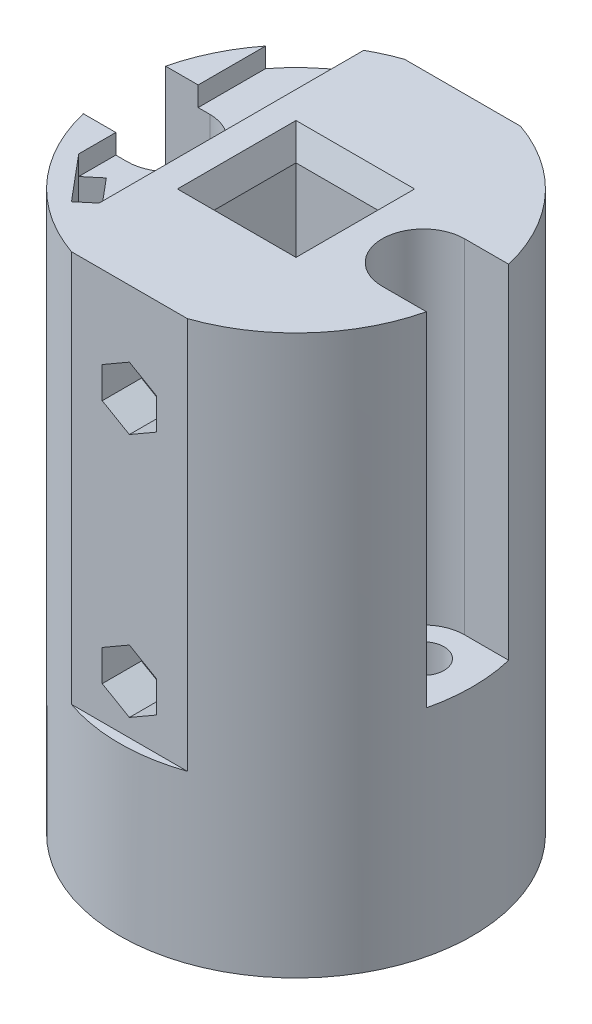
SolidWorks part; units mm, degrees
ref_plane "Спереди" through (0, 0, 0) normal (0, 0, 1) x (1, 0, 0)
ref_plane "Сверху" through (0, 0, 0) normal (0, 1, 0) x (1, 0, 0)
ref_plane "Справа" through (0, 0, 0) normal (1, 0, 0) x (0, 0, -1)
sketch "Sketch1" plane through (0, 0, 0) normal (0, 1, 0) x (1, 0, 0)
  line L0 (0, 0) -> (17.6067, 3.7424) construction
  line L1 (5.05, -5.05) -> (-5.05, -5.05)
  line L2 (5.05, -5.05) -> (5.05, 5.05)
  line L3 (5.05, 5.05) -> (-5.05, 5.05)
  line L4 (-5.05, -5.05) -> (-5.05, 5.05)
  line L5 (5.05, -5.05) -> (-5.05, 5.05) construction
  line L6 (5.05, 5.05) -> (-5.05, -5.05) construction
  line L7 (17.6067, 3.7424) -> (-17.6067, 3.7424) construction
  line L8 (-17.6067, 3.7424) -> (0, 0) construction
  line L9 (-13, 0) -> (13, 0) construction
  circle A0 centre (0, 0) radius 18
  circle A1 centre (13, 0) radius 2.1
  circle A2 centre (-13, 0) radius 2.1
  point P12 (0, 0)
  dimension "D1" = 36
  dimension "D3" = 156
  dimension "D4" = 4.2
  dimension "D2" = 10.1
  dimension "D5" = 26
extrude "Boss-Extrude1" add sketch "Sketch1" along normal blind 57
sketch "Sketch5" plane through (0, 57, 0) normal (0, 1, 0) x (1, 0, 0)
  line L0 (0, 18) -> (0, -18) construction
  line L1 (5.9161, 17) -> (-5.9161, 17)
  line L2 (5.9161, -17) -> (-5.9161, -17)
  circle A0 centre (0, 0) radius 18 construction
  arc A1 (5.9161, 17) -> (-5.9161, 17) centre (0, 0) ccw
  arc A2 (5.9161, -17) -> (-5.9161, -17) centre (0, 0) cw
  point P11 (0, 17)
  dimension "D1" = 1
extrude "Cut-Extrude4" cut sketch "Sketch5" against normal blind 40
sketch "Sketch6" plane through (0, 0, -17) normal (0, 0, -1) x (-1, 0, 0)
  line L0 (0, 57) -> (0, 0) construction
  line L1 (5.9161, 57) -> (-5.9161, 57) construction
  line L2 (5.9161, 17) -> (-5.9161, 17) construction
  line L3 (5.9161, 0) -> (-5.9161, 0) construction
  circle A0 centre (0, 47) radius 1.5
  circle A1 centre (0, 22) radius 1.5
  dimension "D1" = 3
  dimension "D2" = 10
  dimension "D3" = 5
extrude "Cut-Extrude5" cut sketch "Sketch6" against normal through all
sketch "Sketch7" plane through (0, 0, -17) normal (0, 0, -1) x (-1, 0, 0)
  circle A0 centre (0, 47) radius 3
  circle A1 centre (0, 22) radius 3
  dimension "D1" = 6
extrude "Cut-Extrude6" cut sketch "Sketch7" against normal blind 3
sketch "Sketch8" plane through (0, 0, 17) normal (0, 0, 1) x (1, 0, 0)
  line L0 (5.9161, 17) -> (5.9161, 57) construction
  line L1 (0, 43.8) -> (2.7713, 45.4)
  line L2 (2.7713, 45.4) -> (2.7713, 48.6)
  line L3 (2.7713, 48.6) -> (0, 50.2)
  line L4 (0, 50.2) -> (-2.7713, 48.6)
  line L5 (-2.7713, 48.6) -> (-2.7713, 45.4)
  line L6 (-2.7713, 45.4) -> (0, 43.8)
  line L9 (0, 18.8) -> (2.7713, 20.4)
  line L10 (2.7713, 20.4) -> (2.7713, 23.6)
  line L11 (2.7713, 23.6) -> (0, 25.2)
  line L12 (0, 25.2) -> (-2.7713, 23.6)
  line L13 (-2.7713, 23.6) -> (-2.7713, 20.4)
  line L14 (-2.7713, 20.4) -> (0, 18.8)
  circle A0 centre (0, 47) radius 3.2 construction
  circle A1 centre (0, 22) radius 3.2 construction
  dimension "D1" = 6.4
extrude "Cut-Extrude7" cut sketch "Sketch8" against normal blind 4
chamfer "Chamfer1" distance 1 angle 70 4 edges at (-5.05, 57, 0) (0, 57, -5.05) (0, 57, 5.05) (5.05, 57, 0)
sketch "Sketch9" plane through (0, 0, 0) normal (0, -1, 0) x (1, 0, 0)
  line L0 (0, 0) -> (17.6067, -3.7424) construction
  line L1 (17.6067, -3.7424) -> (-17.6067, -3.7424) construction
  line L2 (-17.6067, -3.7424) -> (0, 0) construction
  line L4 (5.05, -5.05) -> (-5.05, -5.05) construction
  line L5 (15.4383, -3.3582) -> (9.4066, -2.0761)
  line L6 (-9.4588, -2.1639) -> (-15.3549, -3.4171)
  circle A0 centre (-13, 0) radius 4.15 construction
  circle A1 centre (13, 0) radius 4.15 construction
  circle A3 centre (0, 0) radius 18 construction
  arc A4 (15.4383, -3.3582) -> (9.4066, -2.0761) centre (13, 0) ccw
  arc A5 (-9.4588, -2.1639) -> (-15.3549, -3.4171) centre (-13, 0) ccw
  dimension "D1" = 8.3
  dimension "D2" = 156
extrude "Cut-Extrude9" cut sketch "Sketch9" against normal blind 6
chamfer "Chamfer2" distance 0.5 angle 70 4 edges at (-13.8628, 0, 4.0593) (-12.4069, 0, -2.7905) (13.8628, 0, 4.0593) (12.4225, 0, -2.7171)
sketch "Sketch10" plane through (0, 57, 0) normal (0, 1, 0) x (1, 0, 0)
  line L0 (13, 4.2) -> (21, 4.2)
  line L1 (21, 4.2) -> (21, -4.2)
  line L2 (21, -4.2) -> (13, -4.2)
  line L3 (-13, 4.2) -> (-21, 4.2)
  line L4 (-21, 4.2) -> (-21, -4.2)
  line L5 (-13, -4.2) -> (-21, -4.2)
  circle A0 centre (13, 0) radius 4.2 construction
  circle A1 centre (-13, 0) radius 4.2 construction
  arc A2 (13, 4.2) -> (13, -4.2) centre (13, 0) ccw
  arc A3 (-13, 4.2) -> (-13, -4.2) centre (-13, 0) cw
  dimension "D1" = 8.4
  dimension "D2" = 8
extrude "Cut-Extrude10" cut sketch "Sketch10" against normal blind 35
sketch "Sketch11" plane through (0, 0, 0) normal (0, -1, 0) x (1, 0, 0)
  line L0 (0, 0) -> (0, 18) construction
  line L1 (0, 0) -> (-13.7888, 11.5702) construction
  line L2 (-14.1851, 7.9865) -> (-10.3283, 12.5827)
  line L3 (-14.1851, 7.9865) -> (-12.653, 6.7009)
  line L4 (-10.3283, 12.5827) -> (-8.7963, 11.2972)
  line L5 (-12.653, 6.7009) -> (-8.7963, 11.2972)
  line L6 (-14.1851, 7.9865) -> (-8.7963, 11.2972) construction
  line L7 (-10.3283, 12.5827) -> (-12.653, 6.7009) construction
  circle A0 centre (0, 0) radius 18 construction
  point P8 (-11.4907, 9.6418)
  dimension "D1" = 50
  dimension "D2" = 6
  dimension "D3" = 2
  dimension "D4" = 3
extrude "Cut-Extrude11" cut sketch "Sketch11" against normal through all
chamfer "Chamfer3" distance 0.5 angle 70 4 edges at (-13.419, 0, 7.3437) (-12.2567, 0, 10.2846) (-10.7246, 0, 8.999) (-9.5623, 0, 11.9399)
sketch "Sketch13" plane through (0, 57, 0) normal (0, 1, 0) x (1, 0, 0)
  line L0 (-8.7963, -11.2972) -> (-8.7963, 15.7043)
  line L1 (-14.1851, -7.9865) -> (-14.1851, 11.0808)
  line L4 (-14.1851, -7.9865) -> (-8.7963, -11.2972)
  arc A1 (-5.9161, 17) -> (-17.5031, 4.2) centre (0, 0) ccw construction
  arc A2 (-8.7963, 15.7043) -> (-14.1851, 11.0808) centre (0, 0) ccw
extrude "Cut-Extrude13" cut sketch "Sketch13" against normal blind 2
